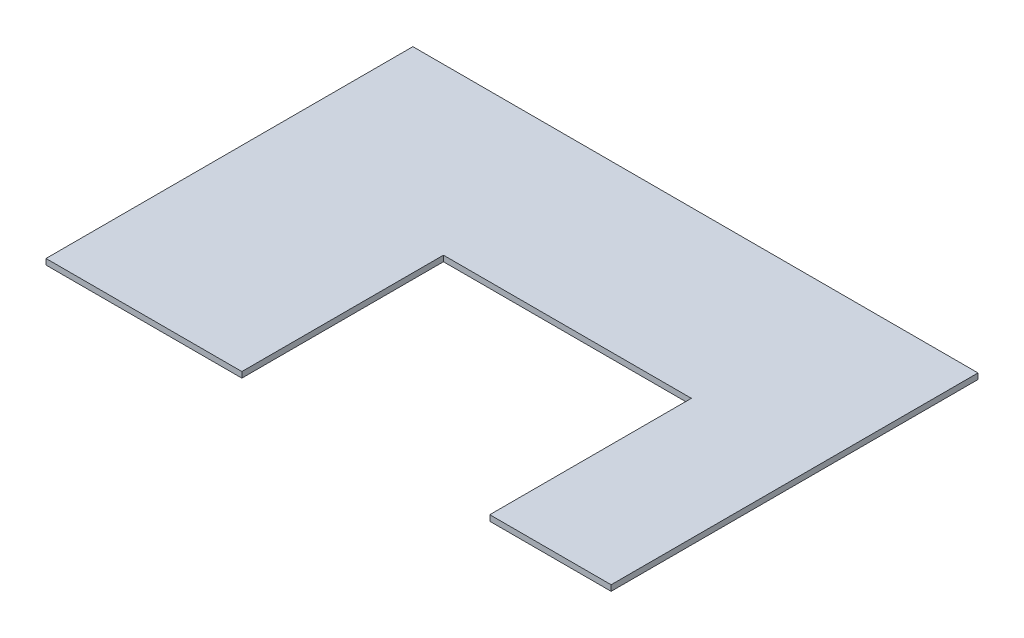
SolidWorks part; units mm, degrees
material "Oak"
ref_plane "Front Plane" through (0, 0, 0) normal (0, 0, 1) x (1, 0, 0)
ref_plane "Top Plane" through (0, 0, 0) normal (0, 1, 0) x (1, 0, 0)
ref_plane "Right Plane" through (0, 0, 0) normal (1, 0, 0) x (0, 0, -1)
sketch "Sketch1" plane through (0, 0, 0) normal (0, 1, 0) x (1, 0, 0)
  line L0 (650.875, 0) -> (650.875, 669.925)
  line L1 (650.875, 669.925) -> (1474.7875, 669.925)
  line L2 (1474.7875, 669.925) -> (1474.7875, 0)
  line L3 (1474.7875, 0) -> (1878.0125, 0)
  line L4 (1878.0125, 0) -> (1878.0125, 1219.2)
  line L5 (1878.0125, 1219.2) -> (0, 1219.2)
  line L6 (0, 1219.2) -> (0, 0)
  line L7 (0, 0) -> (650.875, 0)
  dimension "D1" = 1878.0125
  dimension "D2" = 650.875
  dimension "D3" = 823.9125
  dimension "D4" = 669.925
  dimension "D5" = 1219.2
extrude "Boss-Extrude1" add sketch "Sketch1" against normal blind 19.05
